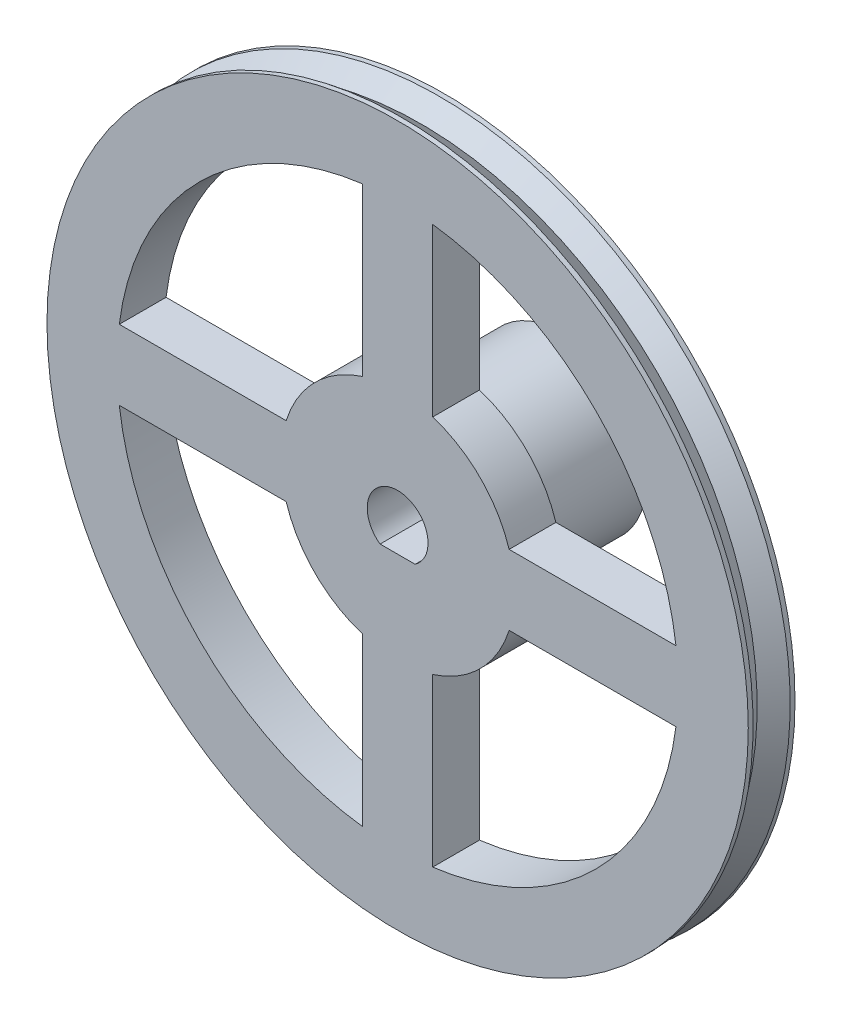
SolidWorks part; units mm, degrees
ref_plane "Alzado" through (0, 0, 0) normal (0, 0, 1) x (1, 0, 0)
ref_plane "Planta" through (0, 0, 0) normal (0, 1, 0) x (1, 0, 0)
ref_plane "Vista lateral" through (0, 0, 0) normal (1, 0, 0) x (0, 0, -1)
sketch "Croquis1" plane through (0, 0, 0) normal (0, 0, 1) x (1, 0, 0)
  circle A0 centre (0, 0) radius 30
  dimension "D1" = 60
extrude "Saliente-Extruir1" add sketch "Croquis1" along normal blind 4
sketch "Croquis3" plane through (0, 0, 0) normal (0, 1, 0) x (1, 0, 0)
  line L0 (-30, 0) -> (-30, -4) construction
  line L1 (-30, -4) -> (-30, -3.5871)
  line L2 (-30, -2) -> (-10.662, -2) construction
  line L3 (-30, 0) -> (-30, -4) construction
  line L4 (-30, -4) -> (-32.4035, -4)
  line L5 (-32.4035, -4) -> (-32.4035, 0)
  line L6 (-32.4035, 0) -> (-30, 0)
  line L7 (30, 0) -> (-30, 0) construction
  line L8 (-30, -0.4129) -> (-30, 0)
  line L9 (-30, -2) -> (-37.0731, -2) construction
  line L10 (-30, -3.5871) -> (-28.759, -2)
  line L11 (-28.759, -2) -> (-30, -0.4129)
  point P2 (-28.759, -2)
  point P8 (-30, -0.6342)
  point P18 (-30, -3.5871)
ref_axis "Eje1" through (0, 0, -0.5007) along (0, 0, 1)
revolve "Cortar-Revolución1" cut sketch "Croquis3" angle 360 about axis through (0, 0, -0.5007) along (0, 0, 1)
sketch "Croquis4" plane through (0, 0, 0) normal (0, 0, -1) x (-1, 0, 0)
  circle A0 centre (0, 0) radius 7.3194
extrude "Saliente-Extruir2" add sketch "Croquis4" along normal blind 10
sketch "Croquis5" plane through (0, 0, 0) normal (0, 0, -1) x (-1, 0, 0)
  line L0 (0, 30) -> (0, -30) construction
  line L1 (-30, 0) -> (30, 0) construction
  line L2 (-23.8118, -3) -> (-9.5394, -3)
  line L3 (-3, -23.8118) -> (-3, -9.5394)
  line L4 (-23.8118, 3) -> (-9.5394, 3)
  line L5 (-3, 23.8118) -> (-3, 9.5394)
  line L6 (3, 23.8118) -> (3, 9.5394)
  line L7 (23.8118, 3) -> (9.5394, 3)
  line L8 (23.8118, -3) -> (9.5394, -3)
  line L9 (3, -23.8118) -> (3, -9.5394)
  circle A0 centre (0, 0) radius 30 construction
  arc A1 (-23.8118, -3) -> (-3, -23.8118) centre (0, 0) ccw
  arc A2 (-9.5394, -3) -> (-3, -9.5394) centre (0, 0) ccw
  arc A3 (-3, 23.8118) -> (-23.8118, 3) centre (0, 0) ccw
  arc A4 (-3, 9.5394) -> (-9.5394, 3) centre (0, 0) ccw
  arc A5 (23.8118, 3) -> (3, 23.8118) centre (0, 0) ccw
  arc A6 (9.5394, 3) -> (3, 9.5394) centre (0, 0) ccw
  arc A7 (3, -23.8118) -> (23.8118, -3) centre (0, 0) ccw
  arc A8 (3, -9.5394) -> (9.5394, -3) centre (0, 0) ccw
  point P12 (-3, -16.6756)
  point P29 (0, 0)
  dimension "D2" = 6
  dimension "D3" = 10
  dimension "D1" = 6
  dimension "D4" = 3
  dimension "D5" = 4
extrude "Cortar-Extruir1" cut sketch "Croquis5" against normal blind 10
sketch "Croquis6" plane through (0, 0, -10) normal (0, 0, -1) x (-1, 0, 0)
  line L0 (1.5, -2.1237) -> (-1.5, -2.1237)
  arc A0 (-1.5, -2.1237) -> (1.5, -2.1237) centre (0, 0) cw
  point P4 (-0.8908, -1.721)
  dimension "D2" = 2.6
  dimension "D1" = 3
extrude "Cortar-Extruir2" cut sketch "Croquis6" against normal through all contours A0 L0
